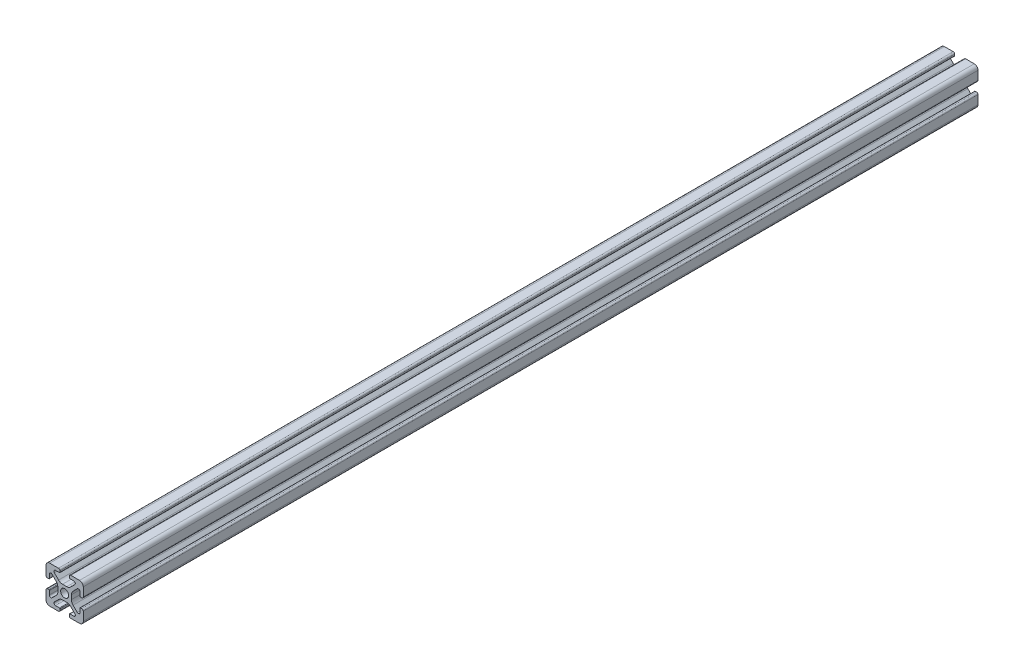
SolidWorks part; units mm, degrees
ref_plane "Front" through (0, 0, 0) normal (0, 0, 1) x (1, 0, 0)
ref_plane "Top" through (0, 0, 0) normal (0, 1, 0) x (1, 0, 0)
ref_plane "Right" through (0, 0, 0) normal (1, 0, 0) x (0, 0, -1)
sketch "Support-Front" plane through (0, 0, 0) normal (0, 0, 1) x (1, 0, 0)
  line L0 (10, 0) -> (-10, 0) construction
  line L1 (-10, -10) -> (10, -10)
  line L2 (-10, -10) -> (-10, 10)
  line L3 (-10, 10) -> (10, 10)
  line L4 (10, -10) -> (10, 10)
  line L5 (0, 10) -> (0, -10) construction
  dimension "Height-Profile" = 20
  dimension "Width-Profile" = 20
sketch "Support-Right-Length" plane through (0, 0, 0) normal (1, 0, 0) x (0, 0, -1)
  line L0 (0, -10) -> (0, 10) construction
  line L1 (-25, 10) -> (25, 10)
  line L2 (-25, 10) -> (-25, -10)
  line L3 (-25, -10) -> (25, -10)
  line L4 (25, 10) -> (25, -10)
  dimension "Length-Profile" = 50
sketch "Support-Profile" plane through (0, 0, 0) normal (0, 0, 1) x (1, 0, 0)
  line L8 (4.9176, -8.2) -> (2.8, -8.2)
  line L9 (2.5, -8.5) -> (2.5, -9.2)
  line L10 (3.3, -10) -> (8, -10)
  line L11 (10, -8) -> (10, -3.3)
  line L24 (9.2, -2.5) -> (8.5, -2.5)
  line L25 (8.2, -2.8) -> (8.2, -4.9176)
  line L26 (6.779, -5.5062) -> (4.5287, -3.2559)
  line L27 (3.65, -1.1346) -> (3.65, 1.1346)
  line L28 (4.5287, 3.2559) -> (6.779, 5.5062)
  line L29 (8.2, 4.9176) -> (8.2, 2.8)
  line L30 (8.5, 2.5) -> (9.2, 2.5)
  line L31 (10, 3.3) -> (10, 8)
  line L32 (8, 10) -> (3.3, 10)
  line L33 (2.5, 9.2) -> (2.5, 8.5)
  line L34 (2.8, 8.2) -> (4.9176, 8.2)
  line L35 (5.5062, 6.779) -> (3.2559, 4.5287)
  line L40 (1.1346, 3.65) -> (-1.1346, 3.65)
  line L41 (-3.2559, 4.5287) -> (-5.5062, 6.779)
  line L42 (-4.9176, 8.2) -> (-2.8, 8.2)
  line L43 (-2.5, 8.5) -> (-2.5, 9.2)
  line L44 (-3.3, 10) -> (-8, 10)
  line L45 (-10, 8) -> (-10, 3.3)
  line L46 (-9.2, 2.5) -> (-8.5, 2.5)
  line L47 (-8.2, 2.8) -> (-8.2, 4.9176)
  line L48 (-6.779, 5.5062) -> (-4.5287, 3.2559)
  line L49 (-3.65, 1.1346) -> (-3.65, -1.1346)
  line L50 (-4.5287, -3.2559) -> (-6.779, -5.5062)
  line L51 (-8.2, -4.9176) -> (-8.2, -2.8)
  line L52 (-8.5, -2.5) -> (-9.2, -2.5)
  line L53 (-10, -3.3) -> (-10, -8)
  line L54 (-8, -10) -> (-3.3, -10)
  line L55 (-2.5, -9.2) -> (-2.5, -8.5)
  line L56 (-2.8, -8.2) -> (-4.9176, -8.2)
  line L57 (-5.5062, -6.779) -> (-3.2559, -4.5287)
  line L58 (-1.1346, -3.65) -> (1.1346, -3.65)
  line L59 (3.2559, -4.5287) -> (5.5062, -6.779)
  circle A2 centre (0, 0) radius 2.15
  arc A3 (2.8, -8.2) -> (2.5, -8.5) centre (2.8, -8.5) ccw
  arc A5 (2.5, -9.2) -> (3.3, -10) centre (3.3, -9.2) ccw
  arc A24 (8, -10) -> (10, -8) centre (8, -8) ccw
  arc A25 (10, -3.3) -> (9.2, -2.5) centre (9.2, -3.3) ccw
  arc A26 (8.5, -2.5) -> (8.2, -2.8) centre (8.5, -2.8) ccw
  arc A27 (6.779, -5.5062) -> (8.2, -4.9176) centre (7.3676, -4.9176) ccw
  arc A28 (3.65, -1.1346) -> (4.5287, -3.2559) centre (6.65, -1.1346) ccw
  arc A29 (4.5287, 3.2559) -> (3.65, 1.1346) centre (6.65, 1.1346) ccw
  arc A30 (8.2, 4.9176) -> (6.779, 5.5062) centre (7.3676, 4.9176) ccw
  arc A31 (8.2, 2.8) -> (8.5, 2.5) centre (8.5, 2.8) ccw
  arc A32 (9.2, 2.5) -> (10, 3.3) centre (9.2, 3.3) ccw
  arc A33 (10, 8) -> (8, 10) centre (8, 8) ccw
  arc A34 (3.3, 10) -> (2.5, 9.2) centre (3.3, 9.2) ccw
  arc A35 (2.5, 8.5) -> (2.8, 8.2) centre (2.8, 8.5) ccw
  arc A38 (5.5062, 6.779) -> (4.9176, 8.2) centre (4.9176, 7.3676) ccw
  arc A39 (1.1346, 3.65) -> (3.2559, 4.5287) centre (1.1346, 6.65) ccw
  arc A44 (-3.2559, 4.5287) -> (-1.1346, 3.65) centre (-1.1346, 6.65) ccw
  arc A45 (-4.9176, 8.2) -> (-5.5062, 6.779) centre (-4.9176, 7.3676) ccw
  arc A46 (-2.8, 8.2) -> (-2.5, 8.5) centre (-2.8, 8.5) ccw
  arc A47 (-2.5, 9.2) -> (-3.3, 10) centre (-3.3, 9.2) ccw
  arc A48 (-8, 10) -> (-10, 8) centre (-8, 8) ccw
  arc A49 (-10, 3.3) -> (-9.2, 2.5) centre (-9.2, 3.3) ccw
  arc A50 (-8.5, 2.5) -> (-8.2, 2.8) centre (-8.5, 2.8) ccw
  arc A51 (-6.779, 5.5062) -> (-8.2, 4.9176) centre (-7.3676, 4.9176) ccw
  arc A52 (-3.65, 1.1346) -> (-4.5287, 3.2559) centre (-6.65, 1.1346) ccw
  arc A53 (-4.5287, -3.2559) -> (-3.65, -1.1346) centre (-6.65, -1.1346) ccw
  arc A54 (-8.2, -4.9176) -> (-6.779, -5.5062) centre (-7.3676, -4.9176) ccw
  arc A55 (-8.2, -2.8) -> (-8.5, -2.5) centre (-8.5, -2.8) ccw
  arc A56 (-9.2, -2.5) -> (-10, -3.3) centre (-9.2, -3.3) ccw
  arc A57 (-10, -8) -> (-8, -10) centre (-8, -8) ccw
  arc A58 (-3.3, -10) -> (-2.5, -9.2) centre (-3.3, -9.2) ccw
  arc A59 (-2.5, -8.5) -> (-2.8, -8.2) centre (-2.8, -8.5) ccw
  arc A60 (-5.5062, -6.779) -> (-4.9176, -8.2) centre (-4.9176, -7.3676) ccw
  arc A61 (-1.1346, -3.65) -> (-3.2559, -4.5287) centre (-1.1346, -6.65) ccw
  arc A62 (3.2559, -4.5287) -> (1.1346, -3.65) centre (1.1346, -6.65) ccw
  arc A63 (4.9176, -8.2) -> (5.5062, -6.779) centre (4.9176, -7.3676) ccw
ref_plane "Ref-Plane-1" through (0, 0, 25) normal (0, 0, 1) x (1, 0, 0)
ref_plane "Ref-Plane-2" through (0, 0, -25) normal (0, 0, 1) x (1, 0, 0)
sketch "Sketch4" plane through (0, 0, 25) normal (0, 0, 1) x (1, 0, 0)
  line L0 (-10, -10) -> (-10, 10) construction
  line L1 (-10, -10) -> (10, -10) construction
  line L2 (10, -10) -> (10, 10) construction
  line L3 (-10, 10) -> (10, 10) construction
  line L4 (-10, -10) -> (-10, 10)
  line L5 (-10, -10) -> (10, -10)
  line L6 (10, -10) -> (10, 10)
  line L7 (-10, 10) -> (10, 10)
extrude "Body" add sketch "Sketch4" against normal blind 480
sketch "Sketch16" plane through (0, 0, 0) normal (0, 0, 1) x (1, 0, 0)
  line L40 (4.9176, -8.2) -> (2.8, -8.2)
  line L41 (2.5, -8.5) -> (2.5, -9.2)
  line L42 (3.3, -10) -> (8, -10)
  line L43 (10, -8) -> (10, -3.3)
  line L44 (9.2, -2.5) -> (8.5, -2.5)
  line L45 (8.2, -2.8) -> (8.2, -4.9176)
  line L46 (6.779, -5.5062) -> (4.5287, -3.2559)
  line L47 (3.65, -1.1346) -> (3.65, 1.1346)
  line L48 (4.5287, 3.2559) -> (6.779, 5.5062)
  line L49 (8.2, 4.9176) -> (8.2, 2.8)
  line L50 (8.5, 2.5) -> (9.2, 2.5)
  line L51 (10, 3.3) -> (10, 8)
  line L52 (8, 10) -> (3.3, 10)
  line L53 (2.5, 9.2) -> (2.5, 8.5)
  line L54 (2.8, 8.2) -> (4.9176, 8.2)
  line L55 (5.5062, 6.779) -> (3.2559, 4.5287)
  line L56 (1.1346, 3.65) -> (-1.1346, 3.65)
  line L57 (-3.2559, 4.5287) -> (-5.5062, 6.779)
  line L58 (-4.9176, 8.2) -> (-2.8, 8.2)
  line L59 (-2.5, 8.5) -> (-2.5, 9.2)
  line L60 (-3.3, 10) -> (-8, 10)
  line L61 (-10, 8) -> (-10, 3.3)
  line L62 (-9.2, 2.5) -> (-8.5, 2.5)
  line L63 (-8.2, 2.8) -> (-8.2, 4.9176)
  line L64 (-6.779, 5.5062) -> (-4.5287, 3.2559)
  line L65 (-3.65, 1.1346) -> (-3.65, -1.1346)
  line L66 (-4.5287, -3.2559) -> (-6.779, -5.5062)
  line L67 (-8.2, -4.9176) -> (-8.2, -2.8)
  line L68 (-8.5, -2.5) -> (-9.2, -2.5)
  line L69 (-10, -3.3) -> (-10, -8)
  line L70 (-8, -10) -> (-3.3, -10)
  line L71 (-2.5, -9.2) -> (-2.5, -8.5)
  line L72 (-2.8, -8.2) -> (-4.9176, -8.2)
  line L73 (-5.5062, -6.779) -> (-3.2559, -4.5287)
  line L74 (-1.1346, -3.65) -> (1.1346, -3.65)
  line L75 (3.2559, -4.5287) -> (5.5062, -6.779)
  line L76 (4.9176, -8.2) -> (2.8, -8.2)
  line L77 (2.5, -8.5) -> (2.5, -9.2)
  line L78 (3.3, -10) -> (8, -10)
  line L79 (10, -8) -> (10, -3.3)
  line L80 (9.2, -2.5) -> (8.5, -2.5)
  line L81 (8.2, -2.8) -> (8.2, -4.9176)
  line L82 (6.779, -5.5062) -> (4.5287, -3.2559)
  line L83 (3.65, -1.1346) -> (3.65, 1.1346)
  line L84 (4.5287, 3.2559) -> (6.779, 5.5062)
  line L85 (8.2, 4.9176) -> (8.2, 2.8)
  line L86 (8.5, 2.5) -> (9.2, 2.5)
  line L87 (10, 3.3) -> (10, 8)
  line L88 (8, 10) -> (3.3, 10)
  line L89 (2.5, 9.2) -> (2.5, 8.5)
  line L90 (2.8, 8.2) -> (4.9176, 8.2)
  line L91 (5.5062, 6.779) -> (3.2559, 4.5287)
  line L92 (1.1346, 3.65) -> (-1.1346, 3.65)
  line L93 (-3.2559, 4.5287) -> (-5.5062, 6.779)
  line L94 (-4.9176, 8.2) -> (-2.8, 8.2)
  line L95 (-2.5, 8.5) -> (-2.5, 9.2)
  line L96 (-3.3, 10) -> (-8, 10)
  line L97 (-10, 8) -> (-10, 3.3)
  line L98 (-9.2, 2.5) -> (-8.5, 2.5)
  line L99 (-8.2, 2.8) -> (-8.2, 4.9176)
  line L100 (-6.779, 5.5062) -> (-4.5287, 3.2559)
  line L101 (-3.65, 1.1346) -> (-3.65, -1.1346)
  line L102 (-4.5287, -3.2559) -> (-6.779, -5.5062)
  line L103 (-8.2, -4.9176) -> (-8.2, -2.8)
  line L104 (-8.5, -2.5) -> (-9.2, -2.5)
  line L105 (-10, -3.3) -> (-10, -8)
  line L106 (-8, -10) -> (-3.3, -10)
  line L107 (-2.5, -9.2) -> (-2.5, -8.5)
  line L108 (-2.8, -8.2) -> (-4.9176, -8.2)
  line L109 (-5.5062, -6.779) -> (-3.2559, -4.5287)
  line L110 (-1.1346, -3.65) -> (1.1346, -3.65)
  line L111 (3.2559, -4.5287) -> (5.5062, -6.779)
  circle A7 centre (0, 0) radius 2.15 construction
  circle A8 centre (0, 0) radius 2.15
  arc A43 (2.8, -8.2) -> (2.5, -8.5) centre (2.8, -8.5) ccw
  arc A44 (2.5, -9.2) -> (3.3, -10) centre (3.3, -9.2) ccw
  arc A45 (8, -10) -> (10, -8) centre (8, -8) ccw
  arc A46 (10, -3.3) -> (9.2, -2.5) centre (9.2, -3.3) ccw
  arc A47 (8.5, -2.5) -> (8.2, -2.8) centre (8.5, -2.8) ccw
  arc A48 (6.779, -5.5062) -> (8.2, -4.9176) centre (7.3676, -4.9176) ccw
  arc A49 (3.65, -1.1346) -> (4.5287, -3.2559) centre (6.65, -1.1346) ccw
  arc A50 (4.5287, 3.2559) -> (3.65, 1.1346) centre (6.65, 1.1346) ccw
  arc A51 (8.2, 4.9176) -> (6.779, 5.5062) centre (7.3676, 4.9176) ccw
  arc A52 (8.2, 2.8) -> (8.5, 2.5) centre (8.5, 2.8) ccw
  arc A53 (9.2, 2.5) -> (10, 3.3) centre (9.2, 3.3) ccw
  arc A54 (10, 8) -> (8, 10) centre (8, 8) ccw
  arc A55 (3.3, 10) -> (2.5, 9.2) centre (3.3, 9.2) ccw
  arc A56 (2.5, 8.5) -> (2.8, 8.2) centre (2.8, 8.5) ccw
  arc A57 (5.5062, 6.779) -> (4.9176, 8.2) centre (4.9176, 7.3676) ccw
  arc A58 (1.1346, 3.65) -> (3.2559, 4.5287) centre (1.1346, 6.65) ccw
  arc A59 (-3.2559, 4.5287) -> (-1.1346, 3.65) centre (-1.1346, 6.65) ccw
  arc A60 (-4.9176, 8.2) -> (-5.5062, 6.779) centre (-4.9176, 7.3676) ccw
  arc A61 (-2.8, 8.2) -> (-2.5, 8.5) centre (-2.8, 8.5) ccw
  arc A62 (-2.5, 9.2) -> (-3.3, 10) centre (-3.3, 9.2) ccw
  arc A63 (-8, 10) -> (-10, 8) centre (-8, 8) ccw
  arc A64 (-10, 3.3) -> (-9.2, 2.5) centre (-9.2, 3.3) ccw
  arc A65 (-8.5, 2.5) -> (-8.2, 2.8) centre (-8.5, 2.8) ccw
  arc A66 (-6.779, 5.5062) -> (-8.2, 4.9176) centre (-7.3676, 4.9176) ccw
  arc A67 (-3.65, 1.1346) -> (-4.5287, 3.2559) centre (-6.65, 1.1346) ccw
  arc A68 (-4.5287, -3.2559) -> (-3.65, -1.1346) centre (-6.65, -1.1346) ccw
  arc A69 (-8.2, -4.9176) -> (-6.779, -5.5062) centre (-7.3676, -4.9176) ccw
  arc A70 (-8.2, -2.8) -> (-8.5, -2.5) centre (-8.5, -2.8) ccw
  arc A71 (-9.2, -2.5) -> (-10, -3.3) centre (-9.2, -3.3) ccw
  arc A72 (-10, -8) -> (-8, -10) centre (-8, -8) ccw
  arc A73 (-3.3, -10) -> (-2.5, -9.2) centre (-3.3, -9.2) ccw
  arc A74 (-2.5, -8.5) -> (-2.8, -8.2) centre (-2.8, -8.5) ccw
  arc A75 (-5.5062, -6.779) -> (-4.9176, -8.2) centre (-4.9176, -7.3676) ccw
  arc A76 (-1.1346, -3.65) -> (-3.2559, -4.5287) centre (-1.1346, -6.65) ccw
  arc A77 (3.2559, -4.5287) -> (1.1346, -3.65) centre (1.1346, -6.65) ccw
  arc A78 (4.9176, -8.2) -> (5.5062, -6.779) centre (4.9176, -7.3676) ccw
  arc A79 (2.8, -8.2) -> (2.5, -8.5) centre (2.8, -8.5) ccw
  arc A80 (2.5, -9.2) -> (3.3, -10) centre (3.3, -9.2) ccw
  arc A81 (8, -10) -> (10, -8) centre (8, -8) ccw
  arc A82 (10, -3.3) -> (9.2, -2.5) centre (9.2, -3.3) ccw
  arc A83 (8.5, -2.5) -> (8.2, -2.8) centre (8.5, -2.8) ccw
  arc A84 (6.779, -5.5062) -> (8.2, -4.9176) centre (7.3676, -4.9176) ccw
  arc A85 (3.65, -1.1346) -> (4.5287, -3.2559) centre (6.65, -1.1346) ccw
  arc A86 (4.5287, 3.2559) -> (3.65, 1.1346) centre (6.65, 1.1346) ccw
  arc A87 (8.2, 4.9176) -> (6.779, 5.5062) centre (7.3676, 4.9176) ccw
  arc A88 (8.2, 2.8) -> (8.5, 2.5) centre (8.5, 2.8) ccw
  arc A89 (9.2, 2.5) -> (10, 3.3) centre (9.2, 3.3) ccw
  arc A90 (10, 8) -> (8, 10) centre (8, 8) ccw
  arc A91 (3.3, 10) -> (2.5, 9.2) centre (3.3, 9.2) ccw
  arc A92 (2.5, 8.5) -> (2.8, 8.2) centre (2.8, 8.5) ccw
  arc A93 (5.5062, 6.779) -> (4.9176, 8.2) centre (4.9176, 7.3676) ccw
  arc A94 (1.1346, 3.65) -> (3.2559, 4.5287) centre (1.1346, 6.65) ccw
  arc A95 (-3.2559, 4.5287) -> (-1.1346, 3.65) centre (-1.1346, 6.65) ccw
  arc A96 (-4.9176, 8.2) -> (-5.5062, 6.779) centre (-4.9176, 7.3676) ccw
  arc A97 (-2.8, 8.2) -> (-2.5, 8.5) centre (-2.8, 8.5) ccw
  arc A98 (-2.5, 9.2) -> (-3.3, 10) centre (-3.3, 9.2) ccw
  arc A99 (-8, 10) -> (-10, 8) centre (-8, 8) ccw
  arc A100 (-10, 3.3) -> (-9.2, 2.5) centre (-9.2, 3.3) ccw
  arc A101 (-8.5, 2.5) -> (-8.2, 2.8) centre (-8.5, 2.8) ccw
  arc A102 (-6.779, 5.5062) -> (-8.2, 4.9176) centre (-7.3676, 4.9176) ccw
  arc A103 (-3.65, 1.1346) -> (-4.5287, 3.2559) centre (-6.65, 1.1346) ccw
  arc A104 (-4.5287, -3.2559) -> (-3.65, -1.1346) centre (-6.65, -1.1346) ccw
  arc A105 (-8.2, -4.9176) -> (-6.779, -5.5062) centre (-7.3676, -4.9176) ccw
  arc A106 (-8.2, -2.8) -> (-8.5, -2.5) centre (-8.5, -2.8) ccw
  arc A107 (-9.2, -2.5) -> (-10, -3.3) centre (-9.2, -3.3) ccw
  arc A108 (-10, -8) -> (-8, -10) centre (-8, -8) ccw
  arc A109 (-3.3, -10) -> (-2.5, -9.2) centre (-3.3, -9.2) ccw
  arc A110 (-2.5, -8.5) -> (-2.8, -8.2) centre (-2.8, -8.5) ccw
  arc A111 (-5.5062, -6.779) -> (-4.9176, -8.2) centre (-4.9176, -7.3676) ccw
  arc A112 (-1.1346, -3.65) -> (-3.2559, -4.5287) centre (-1.1346, -6.65) ccw
  arc A113 (3.2559, -4.5287) -> (1.1346, -3.65) centre (1.1346, -6.65) ccw
  arc A114 (4.9176, -8.2) -> (5.5062, -6.779) centre (4.9176, -7.3676) ccw
  dimension "D1" = 0
extrude "Cut-Profile" cut sketch "Sketch16" against normal through all and the other way through all flip side to cut
